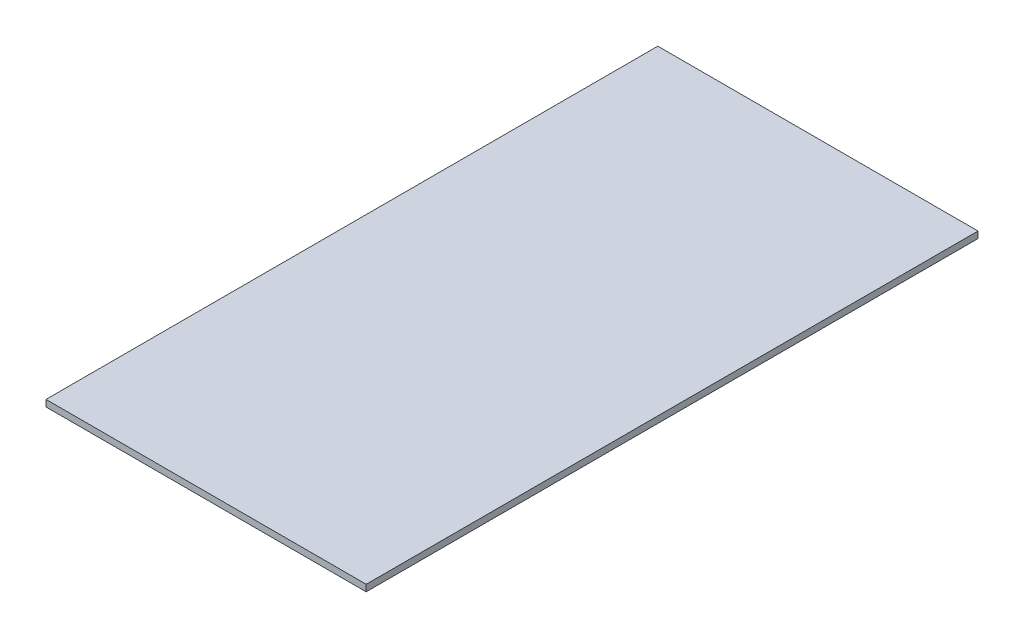
SolidWorks part; units mm, degrees
ref_plane "Front Plane" through (0, 0, 0) normal (0, 0, 1) x (1, 0, 0)
ref_plane "Top Plane" through (0, 0, 0) normal (0, 1, 0) x (1, 0, 0)
ref_plane "Right Plane" through (0, 0, 0) normal (1, 0, 0) x (0, 0, -1)
sketch "Sketch1" plane through (0, 0, 0) normal (0, 1, 0) x (1, 0, 0)
  line L1 (0, 0) -> (146.4056, 0)
  line L2 (0, 0) -> (0, -279.7556)
  line L3 (0, -279.7556) -> (146.4056, -279.7556)
  line L4 (146.4056, 0) -> (146.4056, -279.7556)
  dimension "D1" = 146.4056
  dimension "D2" = 279.7556
extrude "Boss-Extrude1" add sketch "Sketch1" along normal blind 2.9972
